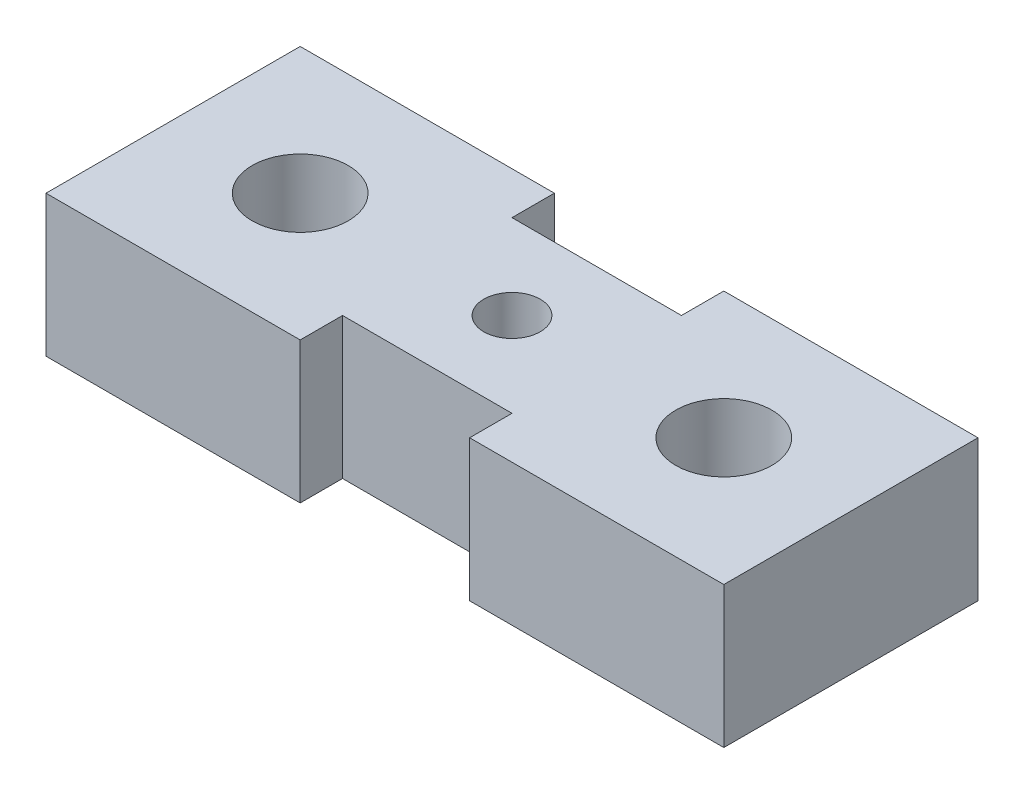
SolidWorks part; units mm, degrees
ref_plane "Front Plane" through (0, 0, 0) normal (0, 0, 1) x (1, 0, 0)
ref_plane "Top Plane" through (0, 0, 0) normal (0, 1, 0) x (1, 0, 0)
ref_plane "Right Plane" through (0, 0, 0) normal (1, 0, 0) x (0, 0, -1)
sketch "Sketch3" plane through (0, 0, 0) normal (0, 1, 0) x (1, 0, 0)
  line L1 (-114.6944, -20.4556) -> (-90.6944, -20.4556)
  line L2 (-114.6944, -20.4556) -> (-114.6944, -29.4556)
  line L3 (-114.6944, -29.4556) -> (-90.6944, -29.4556)
  line L4 (-90.6944, -20.4556) -> (-90.6944, -29.4556)
extrude "Boss-Extrude2" add sketch "Sketch3" along normal blind 5
sketch "Sketch4" plane through (0, 5, 0) normal (0, 1, 0) x (1, 0, 0)
  line L9 (-90.6944, -20.4556) -> (-114.6944, -20.4556) construction
  line L11 (-105.6944, -29.4556) -> (-99.6944, -29.4556)
  line L12 (-105.6944, -29.4556) -> (-105.6944, -27.9556)
  line L13 (-105.6944, -27.9556) -> (-99.6944, -27.9556)
  line L14 (-99.6944, -29.4556) -> (-99.6944, -27.9556)
  line L15 (-105.6944, -20.4556) -> (-99.6944, -20.4556)
  line L16 (-105.6944, -20.4556) -> (-105.6944, -21.9556)
  line L17 (-105.6944, -21.9556) -> (-99.6944, -21.9556)
  line L18 (-99.6944, -20.4556) -> (-99.6944, -21.9556)
  circle A0 centre (-110.1944, -24.9556) radius 1.7
  circle A1 centre (-95.1944, -24.9556) radius 1.7
  circle A2 centre (-102.6944, -24.9556) radius 1
extrude "Cut-Extrude1" cut sketch "Sketch4" against normal blind 5
